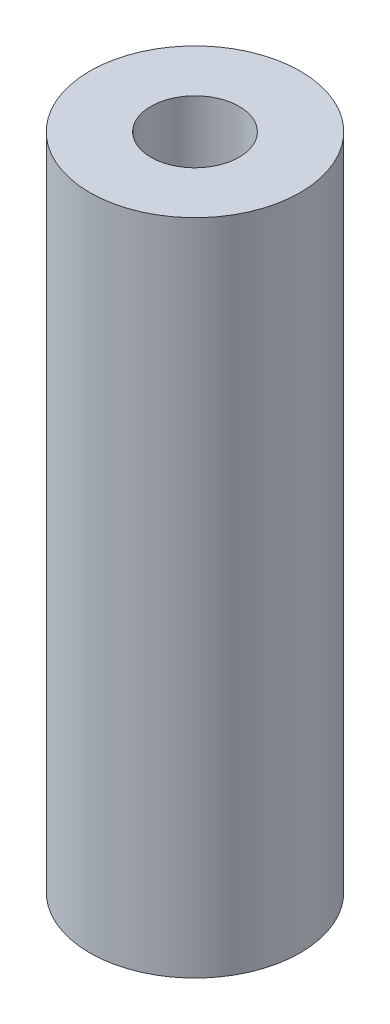
SolidWorks part; units mm, degrees
ref_plane "Front Plane" through (0, 0, 0) normal (0, 0, 1) x (1, 0, 0)
ref_plane "Top Plane" through (0, 0, 0) normal (0, 1, 0) x (1, 0, 0)
ref_plane "Right Plane" through (0, 0, 0) normal (1, 0, 0) x (0, 0, -1)
sketch "Sketch1" plane through (0, 0, 0) normal (0, 1, 0) x (1, 0, 0)
  circle A0 centre (0, 0) radius 6.5
  circle A1 centre (0, 0) radius 15.5
  circle A2 centre (0, 0) radius 4.75
  dimension "D1" = 13
  dimension "D2" = 31
  dimension "D3" = 9.5
extrude "Boss-Extrude1" add sketch "Sketch1" along normal mid plane 97 contours A1 A0
